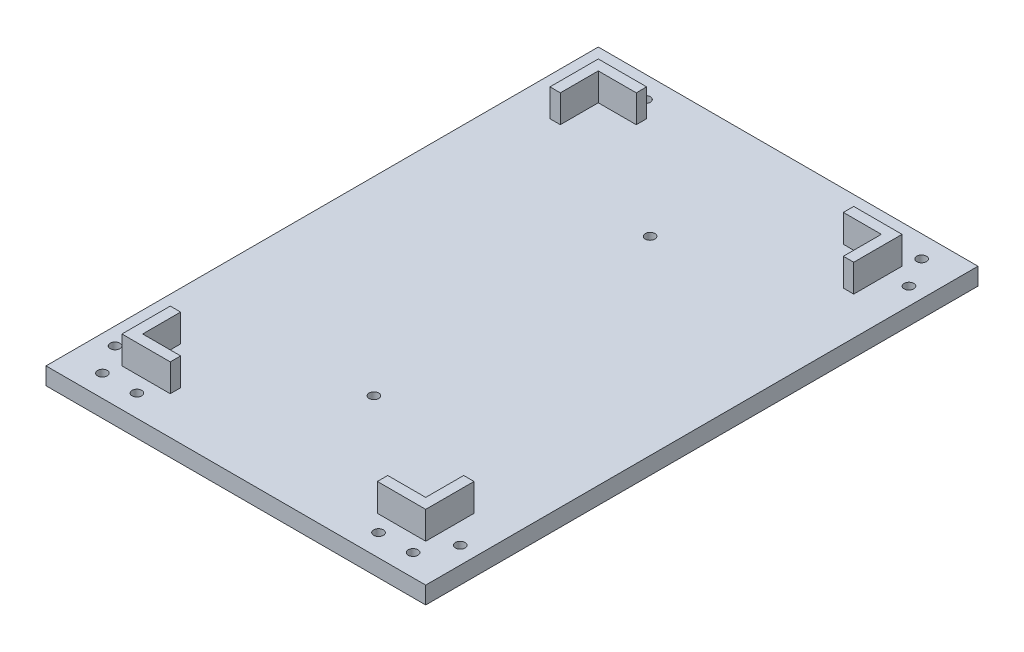
SolidWorks part; units mm, degrees
ref_plane "정면" through (0, 0, 0) normal (0, 0, 1) x (1, 0, 0)
ref_plane "윗면" through (0, 0, 0) normal (0, 1, 0) x (1, 0, 0)
ref_plane "우측면" through (0, 0, 0) normal (1, 0, 0) x (0, 0, -1)
sketch "스케치1" plane through (0, 0, 0) normal (0, 1, 0) x (1, 0, 0)
  line L1 (-55, 80) -> (55, 80)
  line L2 (-55, 80) -> (-55, -80)
  line L3 (-55, -80) -> (55, -80)
  line L4 (55, 80) -> (55, -80)
  line L5 (-55, 80) -> (55, -80) construction
  line L6 (-55, -80) -> (55, 80) construction
  point P0 (0, 0)
  dimension "D1" = 110
  dimension "D2" = 160
extrude "보스-돌출1" add sketch "스케치1" along normal blind 5
sketch "스케치2" plane through (0, 5, 0) normal (0, 1, 0) x (1, 0, 0)
  line L1 (-40, 65) -> (40, 65) construction
  line L2 (-40, 65) -> (-40, -65) construction
  line L3 (-40, -65) -> (40, -65) construction
  line L4 (40, 65) -> (40, -65) construction
  line L5 (-40, 65) -> (40, -65) construction
  line L6 (-40, -65) -> (40, 65) construction
  point P0 (0, 0)
  dimension "D1" = 80
  dimension "D2" = 130
sketch "스케치3" plane through (0, 5, 0) normal (0, 1, 0) x (1, 0, 0)
  line L0 (-40, 65) -> (-40, -65) construction
  line L1 (-50, 65) -> (-40, 65) construction
  line L2 (-40, 65) -> (-45, 73.6603) construction
  line L3 (-40, 65) -> (-35, 73.6603) construction
  line L4 (0, 80) -> (0, -80) construction
  line L5 (55, 80) -> (-55, 80) construction
  line L6 (-55, -80) -> (55, -80) construction
  line L7 (-55, 0) -> (55, 0) construction
  line L8 (-55, 80) -> (-55, -80) construction
  line L9 (55, -80) -> (55, 80) construction
  circle A0 centre (-50, 65) radius 1.4
  circle A1 centre (-45, 73.6603) radius 1.4
  circle A2 centre (-35, 73.6603) radius 1.4
  circle A3 centre (-50, -65) radius 1.4
  circle A4 centre (-45, -73.6603) radius 1.4
  circle A5 centre (-35, -73.6603) radius 1.4
  circle A6 centre (35, 73.6603) radius 1.4
  circle A7 centre (45, 73.6603) radius 1.4
  circle A8 centre (50, 65) radius 1.4
  circle A9 centre (35, -73.6603) radius 1.4
  circle A10 centre (45, -73.6603) radius 1.4
  circle A11 centre (50, -65) radius 1.4
  circle A12 centre (0, 40) radius 1.4
  circle A13 centre (0, -40) radius 1.4
  dimension "D1" = 2.8
  dimension "D5" = 2.8
  dimension "D8" = 2.8
  dimension "D9" = 2.8
  dimension "D10" = 40
  dimension "D2" = 10
  dimension "D3" = 10
  dimension "D4" = 60
  dimension "D6" = 10
  dimension "D7" = 60
extrude "컷-돌출1" cut sketch "스케치3" against normal blind 5
sketch "스케치4" plane through (0, 5, 0) normal (0, 1, 0) x (1, 0, 0)
  line L0 (41, 66) -> (30, 66)
  line L1 (30, 66) -> (30, 69)
  line L2 (30, 69) -> (44, 69)
  line L3 (44, 69) -> (44, 55)
  line L4 (44, 55) -> (41, 55)
  line L5 (41, 66) -> (41, 55)
  line L6 (-40, 65) -> (40, 65) construction
  line L8 (40, 65) -> (40, -65) construction
  line L9 (0, 80) -> (0, -80) construction
  line L10 (55, 80) -> (-55, 80) construction
  line L11 (-55, -80) -> (55, -80) construction
  line L12 (-55, 0) -> (55, 0) construction
  line L13 (-55, 80) -> (-55, -80) construction
  line L14 (55, -80) -> (55, 80) construction
  line L15 (44, -55) -> (41, -55)
  line L16 (44, -69) -> (44, -55)
  line L17 (41, -66) -> (41, -55)
  line L18 (41, -66) -> (30, -66)
  line L19 (30, -69) -> (44, -69)
  line L20 (30, -66) -> (30, -69)
  line L21 (-44, 55) -> (-41, 55)
  line L22 (-30, 66) -> (-30, 69)
  line L23 (-30, 69) -> (-44, 69)
  line L24 (-41, 66) -> (-30, 66)
  line L25 (-41, 66) -> (-41, 55)
  line L26 (-44, 69) -> (-44, 55)
  line L27 (-44, -55) -> (-41, -55)
  line L28 (-41, -66) -> (-41, -55)
  line L29 (-44, -69) -> (-44, -55)
  line L30 (-30, -69) -> (-44, -69)
  line L31 (-41, -66) -> (-30, -66)
  line L32 (-30, -66) -> (-30, -69)
  dimension "D1" = 1
  dimension "D2" = 11
  dimension "D3" = 3
  dimension "D4" = 14
  dimension "D5" = 14
  dimension "D6" = 3
  dimension "D7" = 1
extrude "보스-돌출2" add sketch "스케치4" along normal blind 8
sketch "스케치5" plane through (0, 0, 0) normal (0, -1, 0) x (1, 0, 0)
  circle A0 centre (0, 40) radius 3
  circle A1 centre (0, -40) radius 3
  dimension "D1" = 6
  dimension "D2" = 6
extrude "컷-돌출2" cut sketch "스케치5" against normal blind 2.5
